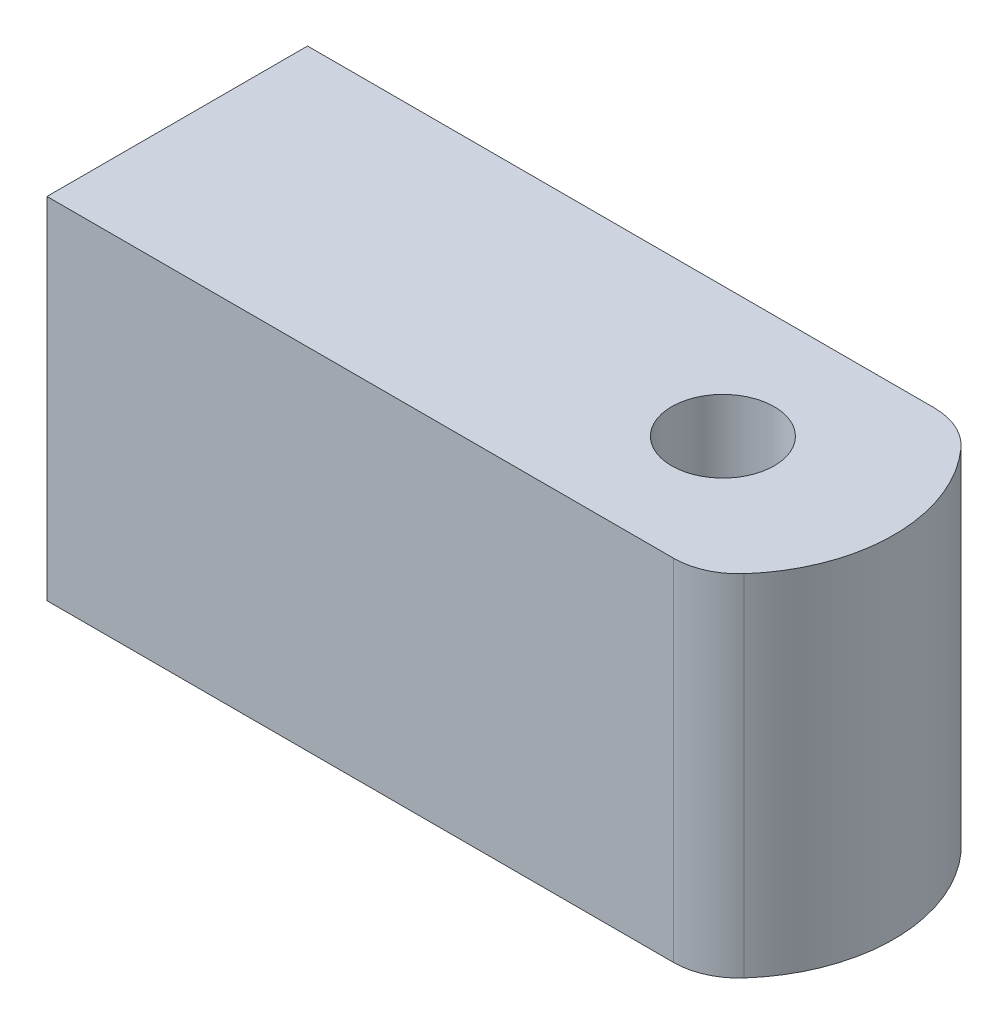
SolidWorks part; units mm, degrees
ref_plane "Front Plane" through (0, 0, 0) normal (0, 0, 1) x (1, 0, 0)
ref_plane "Top Plane" through (0, 0, 0) normal (0, 1, 0) x (1, 0, 0)
ref_plane "Right Plane" through (0, 0, 0) normal (1, 0, 0) x (0, 0, -1)
sketch "Sketch1" plane through (0, 0, 0) normal (0, 1, 0) x (1, 0, 0)
  line L0 (0, 0) -> (0, 16)
  line L1 (0, 16) -> (25.0051, 16)
  line L2 (0, 0) -> (25.0051, 0)
  arc A1 (25.0051, 0) -> (25.0051, 16) centre (19.0051, 8) ccw
extrude "Boss-Extrude1" add sketch "Sketch1" along normal blind 19 and the other way blind 4
sketch "Sketch2" plane through (0, 19, 0) normal (0, 1, 0) x (1, 0, 0)
  circle A0 centre (18.5051, 8) radius 3.15
extrude "Cut-Extrude1" cut sketch "Sketch2" against normal blind 32
sketch "Sketch3" plane through (0, 0, 0) normal (-1, 0, 0) x (0, 0, 1)
  line L3 (-2.75, 2.75) -> (-13.25, 2.75)
  line L4 (-13.25, 2.75) -> (-13.25, 13.25)
  line L5 (-13.25, 13.25) -> (-2.75, 13.25)
  line L6 (-2.75, 13.25) -> (-2.75, 2.75)
extrude "Cut-Extrude2" cut sketch "Sketch3" against normal blind 24
fillet "Fillet1" radius 4 2 edges at (25.0051, 7.5, 0) (25.0051, 7.5, -16)
sketch "Sketch4" plane through (0, 0, 0) normal (-1, 0, 0) x (0, 0, 1)
  line L1 (-16, 19) -> (0, 19)
  line L4 (-13.25, 2.75) -> (-13.25, 13.25)
  line L5 (-13.25, 13.25) -> (-2.75, 13.25)
  line L6 (-2.75, 13.25) -> (-2.75, 2.75)
  line L7 (-2.75, 2.75) -> (-13.25, 2.75)
  line L8 (-16, 19) -> (-16, -4)
  line L9 (-16, -4) -> (0, -4)
  line L10 (0, -4) -> (0, 19)
extrude "Boss-Extrude2" add sketch "Sketch4" along normal blind 15
sketch "Sketch5" plane through (-15, 0, 0) normal (-1, 0, 0) x (0, 0, 1)
  line L1 (-16, 19) -> (-16, -4) construction
  line L3 (-16, -2.75) -> (-16, -4)
  line L4 (-16, -4) -> (0, -4)
  line L5 (-16, -2.75) -> (0, -2.75)
  line L6 (0, -4) -> (0, 19) construction
  line L7 (0, -2.75) -> (0, 18.75)
  line L8 (0, 18.75) -> (-16, 18.75)
  line L9 (0, -4) -> (0, -2.75)
  line L12 (0, 18.75) -> (0, 19)
  line L13 (0, 19) -> (-16, 19)
  line L14 (-16, 19) -> (-16, 18.75)
  line M3 (-16, -4) -> (0, -4)
  line M4 (0, -4) -> (0, 19)
  line M6 (-16, 19) -> (-16, -4)
extrude "Cut-Extrude3" cut sketch "Sketch5" against normal blind 48 contours L5 M6 M3 M4 | L12 L13 L14 L8
sketch "Sketch6" plane through (0, 18.75, 0) normal (0, 1, 0) x (1, 0, 0)
  line L0 (15.3551, 8) -> (15.3551, 16)
  line L1 (23.4773, 16) -> (-15, 16) construction
  circle A0 centre (18.5051, 8) radius 3.15 construction
sketch3d "3DSketch1"
  line L0 (15.3551, 18.75, -8) -> (15.3551, 18.75, -16) construction
